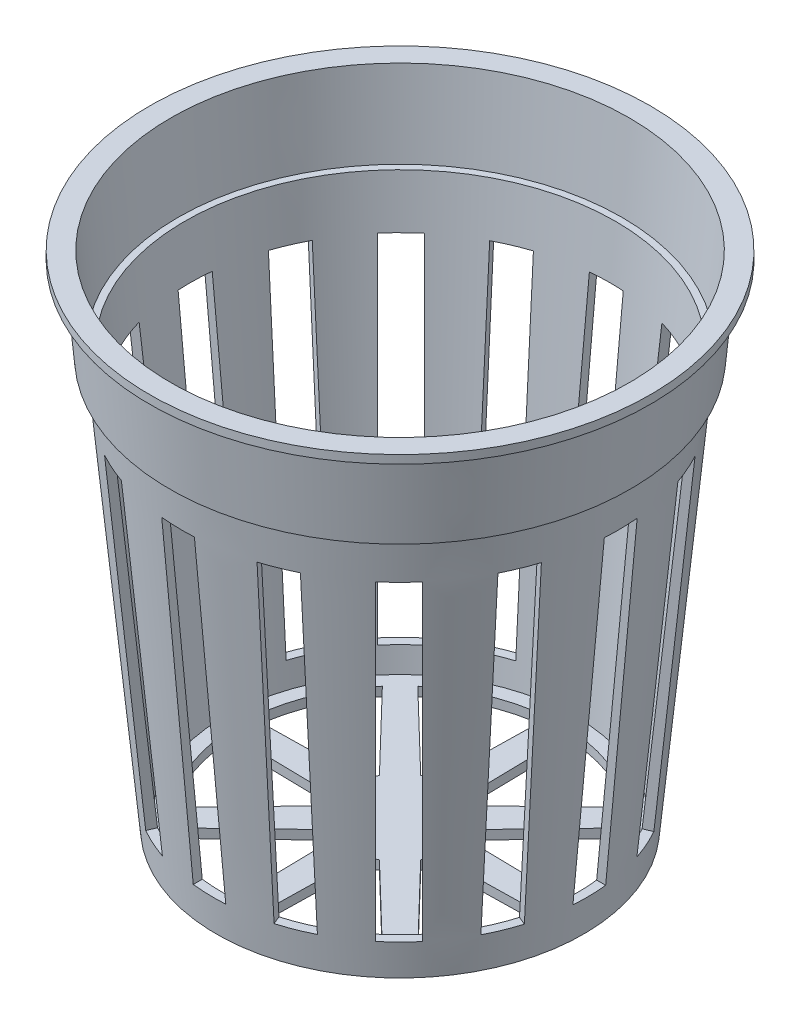
SolidWorks part; units mm, degrees
ref_plane "Alzado" through (0, 0, 0) normal (0, 0, 1) x (1, 0, 0)
ref_plane "Planta" through (0, 0, 0) normal (0, 1, 0) x (1, 0, 0)
ref_plane "Vista lateral" through (0, 0, 0) normal (1, 0, 0) x (0, 0, -1)
sketch "Croquis1" plane through (0, 0, 0) normal (0, 0, 1) x (1, 0, 0)
  line L0 (-27.4894, 0) -> (-30, 0)
  line L1 (-30, 0) -> (-30, -1)
  line L2 (-30, -1) -> (-28.5, -1)
  line L3 (-28.5, -1) -> (-27.6034, -11)
  line L4 (-27.6034, -11) -> (-26.6034, -11)
  line L5 (-26.6034, -11) -> (-22, -60)
  line L6 (-22, -60) -> (0, -60)
  line L7 (0, -60) -> (0, -58.9025)
  line L8 (0, -58.9025) -> (-21.02, -58.9025)
  line L9 (-21.02, -58.9025) -> (-25.8044, -9.8819)
  line L10 (-25.8044, -9.8819) -> (-26.6034, -9.8819)
  line L11 (-26.6034, -9.8819) -> (-27.4894, 0)
  dimension "D2" = 1
  dimension "D3" = 1.5
  dimension "D4" = 22
  dimension "D5" = 1
  dimension "D7" = 10
revolve "Revolución1" add sketch "Croquis1" angle 360 about L7
sketch "Croquis9" plane through (0, 0, 0) normal (0, 1, 0) x (1, 0, 0)
  line L0 (-1.75, 6.1847) -> (-1.5, 19.3001)
  line L1 (3.1358, 5.6107) -> (12.5866, 14.7079)
  line L2 (1.75, 6.1847) -> (1.5, 19.3001)
  line L3 (6.1847, 1.75) -> (19.3001, 1.5)
  line L4 (5.6107, 3.1358) -> (14.7079, 12.5866)
  line L5 (5.6107, -3.1358) -> (14.7079, -12.5866)
  line L6 (6.1847, -1.75) -> (19.3001, -1.5)
  line L7 (1.75, -6.1847) -> (1.5, -19.3001)
  line L8 (3.1358, -5.6107) -> (12.5866, -14.7079)
  line L9 (-3.1358, -5.6107) -> (-12.5866, -14.7079)
  line L10 (-1.75, -6.1847) -> (-1.5, -19.3001)
  line L11 (-6.1847, -1.75) -> (-19.3001, -1.5)
  line L12 (-5.6107, -3.1358) -> (-14.7079, -12.5866)
  line L13 (-5.6107, 3.1358) -> (-14.7079, 12.5866)
  line L14 (-3.1358, 5.6107) -> (-12.5866, 14.7079)
  line L15 (-6.1847, 1.75) -> (-19.3001, 1.5)
  arc A0 (12.5866, 14.7079) -> (1.5, 19.3001) centre (0, 0) ccw
  arc A1 (1.75, 6.1847) -> (3.1358, 5.6107) centre (0, 0) cw
  arc A2 (-1.5, 19.3001) -> (-12.5866, 14.7079) centre (0, 0) ccw
  arc A3 (-3.1358, 5.6107) -> (-1.75, 6.1847) centre (0, 0) cw
  arc A4 (19.3001, 1.5) -> (14.7079, 12.5866) centre (0, 0) ccw
  arc A5 (5.6107, 3.1358) -> (6.1847, 1.75) centre (0, 0) cw
  arc A6 (14.7079, -12.5866) -> (19.3001, -1.5) centre (0, 0) ccw
  arc A7 (6.1847, -1.75) -> (5.6107, -3.1358) centre (0, 0) cw
  arc A8 (1.5, -19.3001) -> (12.5866, -14.7079) centre (0, 0) ccw
  arc A9 (3.1358, -5.6107) -> (1.75, -6.1847) centre (0, 0) cw
  arc A10 (-12.5866, -14.7079) -> (-1.5, -19.3001) centre (0, 0) ccw
  arc A11 (-1.75, -6.1847) -> (-3.1358, -5.6107) centre (0, 0) cw
  arc A12 (-19.3001, -1.5) -> (-14.7079, -12.5866) centre (0, 0) ccw
  arc A13 (-5.6107, -3.1358) -> (-6.1847, -1.75) centre (0, 0) cw
  arc A14 (-14.7079, 12.5866) -> (-19.3001, 1.5) centre (0, 0) ccw
  arc A15 (-6.1847, 1.75) -> (-5.6107, 3.1358) centre (0, 0) cw
  point P38 (0, 0)
  dimension "D3" = 8
  dimension "D17" = 1.5
  dimension "D25" = 12
extrude "Cortar-Extruir2" cut sketch "Croquis9" against normal blind 112
sketch "Croquis10" plane through (0, 0, 0) normal (0, 0, 1) x (1, 0, 0)
  line L0 (0, -60) -> (0, -56)
  line L1 (-22, -60) -> (22, -60) construction
  dimension "D1" = 4
ref_plane "Plano2" through (0, -56, 0) normal (0, 1, 0) x (1, 0, 0)
sketch "Croquis11" plane through (0, -56, 0) normal (0, 1, 0) x (1, 0, 0)
  line L0 (1.75, 6.1847) -> (1.5, 19.3001) construction
  line L1 (-2.4, 30.862) -> (1.6, 30.862)
  line L2 (-2.4, 30.862) -> (-2.4, 14.0539)
  line L3 (-2.4, 14.0539) -> (1.6, 14.0539)
  line L4 (1.6, 30.862) -> (1.6, 14.0539)
  line L5 (-2.4, 30.862) -> (1.6, 14.0539) construction
  line L6 (-2.4, 14.0539) -> (1.6, 30.862) construction
  line L7 (9.3727, 29.284) -> (2.9405, 13.7553)
  line L8 (13.0682, 27.7533) -> (6.636, 12.2246)
  line L9 (9.3727, 29.284) -> (13.0682, 27.7533)
  line L10 (2.9405, 13.7553) -> (6.636, 12.2246)
  line L11 (19.6454, 23.3208) -> (7.7603, 11.4357)
  line L12 (22.4738, 20.4924) -> (10.5887, 8.6073)
  line L13 (19.6454, 23.3208) -> (22.4738, 20.4924)
  line L14 (7.7603, 11.4357) -> (10.5887, 8.6073)
  line L15 (26.8541, 13.8804) -> (11.3254, 7.4483)
  line L16 (28.3848, 10.1849) -> (12.8562, 3.7528)
  line L17 (26.8541, 13.8804) -> (28.3848, 10.1849)
  line L18 (11.3254, 7.4483) -> (12.8562, 3.7528)
  line L19 (29.9014, 2.4) -> (13.0933, 2.4)
  line L20 (29.9014, -1.6) -> (13.0933, -1.6)
  line L21 (29.9014, 2.4) -> (29.9014, -1.6)
  line L22 (13.0933, 2.4) -> (13.0933, -1.6)
  line L23 (28.3234, -9.3727) -> (12.7947, -2.9405)
  line L24 (26.7926, -13.0682) -> (11.264, -6.636)
  line L25 (28.3234, -9.3727) -> (26.7926, -13.0682)
  line L26 (12.7947, -2.9405) -> (11.264, -6.636)
  line L27 (22.3602, -19.6454) -> (10.4751, -7.7603)
  line L28 (19.5318, -22.4738) -> (7.6467, -10.5887)
  line L29 (22.3602, -19.6454) -> (19.5318, -22.4738)
  line L30 (10.4751, -7.7603) -> (7.6467, -10.5887)
  line L31 (12.9198, -26.8541) -> (6.4876, -11.3254)
  line L32 (9.2243, -28.3848) -> (2.7921, -12.8562)
  line L33 (12.9198, -26.8541) -> (9.2243, -28.3848)
  line L34 (6.4876, -11.3254) -> (2.7921, -12.8562)
  line L35 (1.4394, -29.9014) -> (1.4394, -13.0933)
  line L36 (-2.5606, -29.9014) -> (-2.5606, -13.0933)
  line L37 (1.4394, -29.9014) -> (-2.5606, -29.9014)
  line L38 (1.4394, -13.0933) -> (-2.5606, -13.0933)
  line L39 (-10.3333, -28.3234) -> (-3.9012, -12.7947)
  line L40 (-14.0289, -26.7926) -> (-7.5967, -11.264)
  line L41 (-10.3333, -28.3234) -> (-14.0289, -26.7926)
  line L42 (-3.9012, -12.7947) -> (-7.5967, -11.264)
  line L43 (-20.606, -22.3602) -> (-8.7209, -10.4751)
  line L44 (-23.4344, -19.5318) -> (-11.5493, -7.6467)
  line L45 (-20.606, -22.3602) -> (-23.4344, -19.5318)
  line L46 (-8.7209, -10.4751) -> (-11.5493, -7.6467)
  line L47 (-27.8147, -12.9198) -> (-12.2861, -6.4876)
  line L48 (-29.3455, -9.2243) -> (-13.8168, -2.7921)
  line L49 (-27.8147, -12.9198) -> (-29.3455, -9.2243)
  line L50 (-12.2861, -6.4876) -> (-13.8168, -2.7921)
  line L51 (-30.862, -1.4394) -> (-14.0539, -1.4394)
  line L52 (-30.862, 2.5606) -> (-14.0539, 2.5606)
  line L53 (-30.862, -1.4394) -> (-30.862, 2.5606)
  line L54 (-14.0539, -1.4394) -> (-14.0539, 2.5606)
  line L55 (-29.284, 10.3333) -> (-13.7553, 3.9012)
  line L56 (-27.7533, 14.0289) -> (-12.2246, 7.5967)
  line L57 (-29.284, 10.3333) -> (-27.7533, 14.0289)
  line L58 (-13.7553, 3.9012) -> (-12.2246, 7.5967)
  line L59 (-23.3208, 20.606) -> (-11.4357, 8.7209)
  line L60 (-20.4924, 23.4344) -> (-8.6073, 11.5493)
  line L61 (-23.3208, 20.606) -> (-20.4924, 23.4344)
  line L62 (-11.4357, 8.7209) -> (-8.6073, 11.5493)
  line L63 (-13.8804, 27.8147) -> (-7.4483, 12.2861)
  line L64 (-10.1849, 29.3455) -> (-3.7528, 13.8168)
  line L65 (-13.8804, 27.8147) -> (-10.1849, 29.3455)
  line L66 (-7.4483, 12.2861) -> (-3.7528, 13.8168)
  point P0 (-0.4, 22.458)
  point P69 (-0.4803, 0.4803)
  dimension "D1" = 4
  dimension "D3" = 1.6
  dimension "D2" = 16
extrude "Cortar-Extruir3" cut sketch "Croquis11" along normal blind 40
